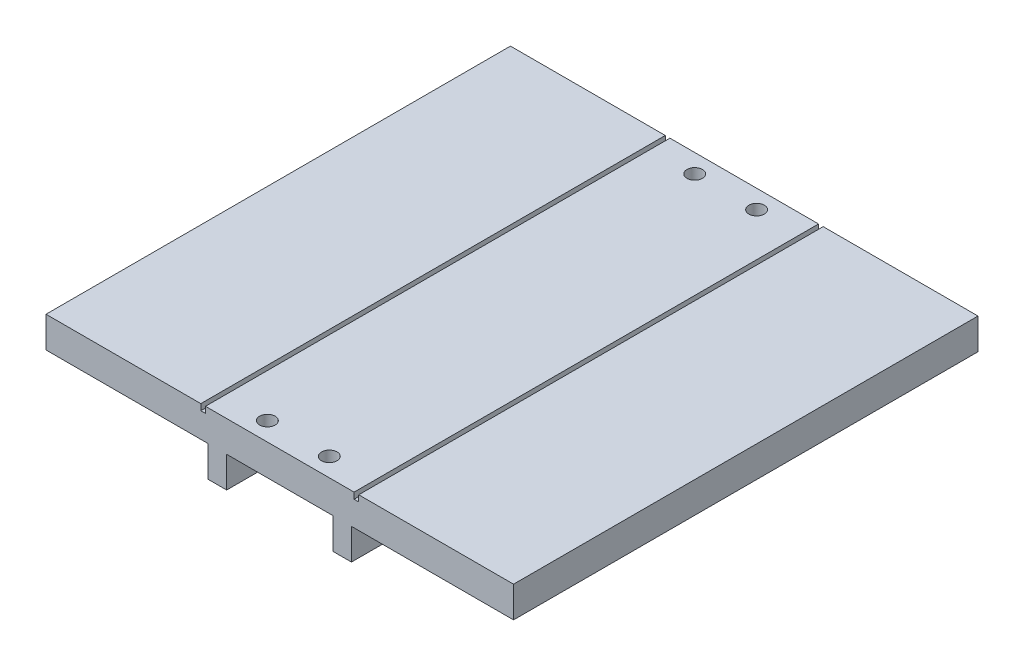
SolidWorks part; units mm, degrees
ref_plane "Front Plane" through (0, 0, 0) normal (0, 0, 1) x (1, 0, 0)
ref_plane "Top Plane" through (0, 0, 0) normal (0, 1, 0) x (1, 0, 0)
ref_plane "Right Plane" through (0, 0, 0) normal (1, 0, 0) x (0, 0, -1)
sketch "Sketch1" plane through (0, 0, 0) normal (0, 0, 1) x (1, 0, 0)
  line L0 (0, 5) -> (0, -5) construction
  line L1 (-75.5, 5) -> (75.5, 5)
  line L2 (-75.5, 5) -> (-75.5, -5)
  line L3 (-75.5, -5) -> (-23.1515, -5)
  line L4 (75.5, 5) -> (75.5, -5)
  line L5 (-75.5, 5) -> (75.5, -5) construction
  line L6 (-75.5, -5) -> (75.5, 5) construction
  line L7 (17.1515, -5) -> (17.1515, -15)
  line L8 (17.1515, -15) -> (23.1515, -15)
  line L9 (23.1515, -15) -> (23.1515, -5)
  line L10 (-23.1515, -15) -> (-23.1515, -5)
  line L11 (-17.1515, -15) -> (-23.1515, -15)
  line L12 (-17.1515, -5) -> (-17.1515, -15)
  line L13 (-17.1515, -5) -> (17.1515, -5)
  line L14 (23.1515, -5) -> (75.5, -5)
  point P0 (0, 0)
  dimension "D1" = 10
  dimension "D2" = 151
  dimension "D3" = 6
  dimension "D4" = 10
  dimension "D5" = 23.1515
  dimension "D6" = 23.1515
  dimension "D7" = 6
  dimension "D8" = 10
extrude "Boss-Extrude1" add sketch "Sketch1" along normal blind 150
sketch "Sketch4" plane through (0, -5, 0) normal (0, -1, 0) x (1, 0, 0)
  line L0 (0, 150) -> (0, 0) construction
  line L1 (-17.1515, 150) -> (17.1515, 150) construction
  line L2 (-17.1515, 144) -> (17.1515, 144) construction
  line L3 (-17.1515, 150) -> (-17.1515, 0) construction
  line L4 (17.1515, 150) -> (17.1515, 0) construction
  line L5 (-17.1515, 6) -> (17.1515, 6) construction
  line L6 (-10, 150) -> (-10, 0) construction
  line L7 (-17.1515, 0) -> (17.1515, 0) construction
  line L8 (10, 150) -> (10, 0) construction
  circle A0 centre (-10, 6) radius 1.65
  circle A1 centre (10, 6) radius 1.65
  circle A2 centre (-10, 144) radius 1.65
  circle A3 centre (10, 144) radius 1.65
  dimension "D4" = 3.3
  dimension "D5" = 3.3
  dimension "D1" = 6
  dimension "D2" = 6
  dimension "D3" = 10
  dimension "D6" = 34.3029
extrude "Cut-Extrude1" cut sketch "Sketch4" against normal up to surface (10 mm away) up to face at (0, 5, 75)
sketch "Sketch6" plane through (0, 5, 0) normal (0, 1, 0) x (1, 0, 0)
  line L0 (75.5, 0) -> (-75.5, 0) construction
  line L1 (-25.5, 0) -> (-24, 0)
  line L2 (-25.5, 0) -> (-25.5, -150)
  line L3 (-25.5, -150) -> (-24, -150)
  line L4 (-24, 0) -> (-24, -150)
  line L5 (75.5, -150) -> (-75.5, -150) construction
  line L6 (-75.5, -150) -> (-75.5, 0) construction
  line L7 (75.5, -150) -> (75.5, 0) construction
  line L8 (25.5, 0) -> (24, 0)
  line L9 (25.5, 0) -> (25.5, -150)
  line L10 (25.5, -150) -> (24, -150)
  line L11 (24, 0) -> (24, -150)
  dimension "D1" = 1.5
  dimension "D2" = 50
  dimension "D3" = 1.5
  dimension "D4" = 50
extrude "Cut-Extrude2" cut sketch "Sketch6" against normal blind 2
sketch "Sketch7" plane through (0, 5, 0) normal (0, 1, 0) x (1, 0, 0)
  line L0 (-10, -4.35) -> (-10, -7.65) construction
  line L1 (-11.65, -6) -> (-8.35, -6) construction
  circle A0 centre (-10, -144) radius 2.5
  circle A1 centre (10, -144) radius 2.5
  circle A2 centre (-10, -6) radius 1.65 construction
  circle A3 centre (10, -6) radius 2.5
  circle A4 centre (-10, -6) radius 2.5
  dimension "D1" = 5
  dimension "D2" = 5
  dimension "D3" = 5
  dimension "D4" = 5
extrude "Cut-Extrude3" cut sketch "Sketch7" against normal blind 7
